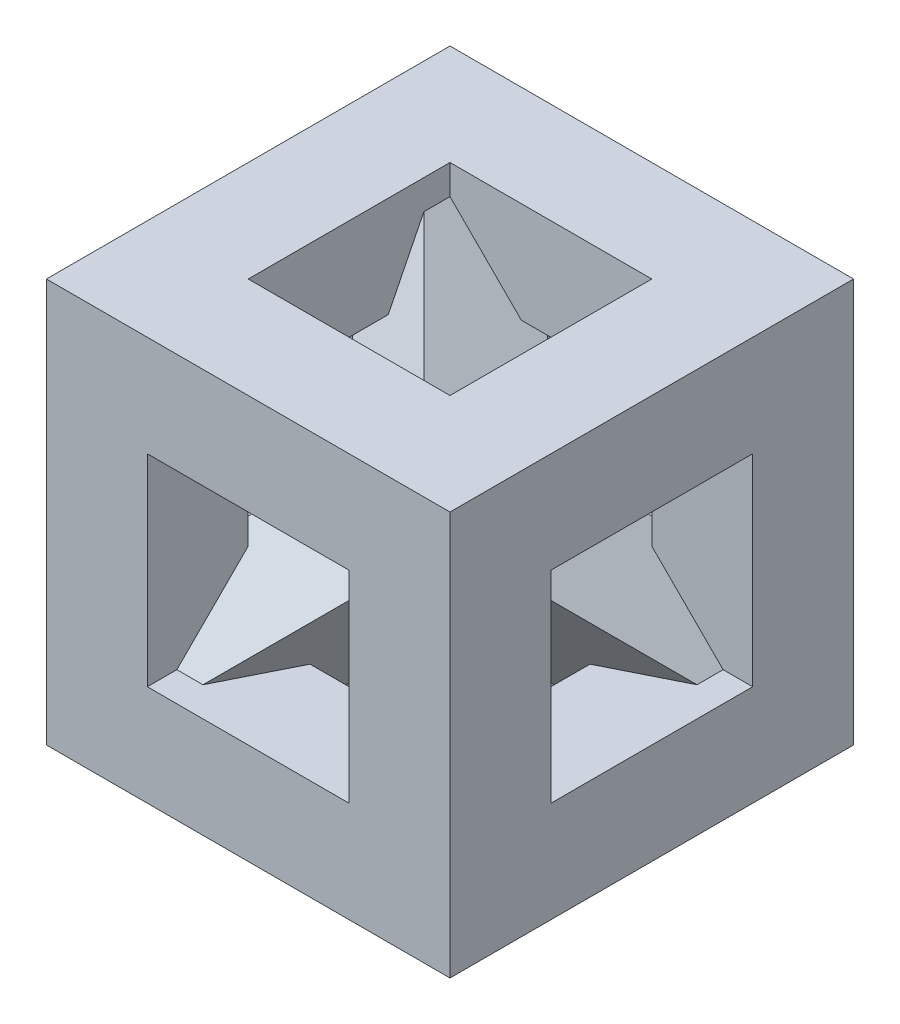
SolidWorks part; units mm, degrees
ref_plane "Front Plane" through (0, 0, 0) normal (0, 0, 1) x (1, 0, 0)
ref_plane "Top Plane" through (0, 0, 0) normal (0, 1, 0) x (1, 0, 0)
ref_plane "Right Plane" through (0, 0, 0) normal (1, 0, 0) x (0, 0, -1)
sketch "Sketch1" plane through (0, 0, 0) normal (0, 0, 1) x (1, 0, 0)
  line L1 (-5, 5) -> (5, 5)
  line L2 (-5, 5) -> (-5, -5)
  line L3 (-5, -5) -> (5, -5)
  line L4 (5, 5) -> (5, -5)
  line L5 (-5, 5) -> (5, -5) construction
  line L6 (-5, -5) -> (5, 5) construction
  point P0 (0, 0)
  dimension "D1" = 10
  dimension "D2" = 10
extrude "Boss-Extrude1" add sketch "Sketch1" along normal blind 10
sketch "Sketch2" plane through (0, 0, 10) normal (0, 0, 1) x (1, 0, 0)
  line L1 (-2.5, 2.5) -> (2.5, 2.5)
  line L2 (-2.5, 2.5) -> (-2.5, -2.5)
  line L3 (-2.5, -2.5) -> (2.5, -2.5)
  line L4 (2.5, 2.5) -> (2.5, -2.5)
  line L5 (-2.5, 2.5) -> (2.5, -2.5) construction
  line L6 (-2.5, -2.5) -> (2.5, 2.5) construction
  point P0 (0, 0)
  dimension "D1" = 5
extrude "Cut-Extrude1" cut sketch "Sketch2" against normal blind 13
sketch "Sketch3" plane through (5, 0, 0) normal (1, 0, 0) x (0, 0, -1)
  line L0 (0, -5) -> (0, 5) construction
  line L1 (-7.5, 2.5) -> (-2.5, 2.5)
  line L2 (-7.5, 2.5) -> (-7.5, -2.5)
  line L3 (-7.5, -2.5) -> (-2.5, -2.5)
  line L4 (-2.5, 2.5) -> (-2.5, -2.5)
  line L5 (-7.5, 2.5) -> (-2.5, -2.5) construction
  line L6 (-7.5, -2.5) -> (-2.5, 2.5) construction
  line L8 (-10, -5) -> (0, -5) construction
  point P0 (-5, 0)
  dimension "D1" = 5
  dimension "D2" = 2.5
  dimension "D3" = 2.5
extrude "Cut-Extrude2" cut sketch "Sketch3" against normal blind 13
sketch "Sketch4" plane through (0, 5, 0) normal (0, 1, 0) x (1, 0, 0)
  line L0 (5, -10) -> (-5, -10) construction
  line L2 (-5, -10) -> (-5, 0) construction
  line L7 (-2.5, -2.5) -> (2.5, -2.5)
  line L8 (-2.5, -2.5) -> (-2.5, -7.5)
  line L9 (-2.5, -7.5) -> (2.5, -7.5)
  line L10 (2.5, -2.5) -> (2.5, -7.5)
  line L11 (-2.5, -2.5) -> (2.5, -7.5) construction
  line L12 (-2.5, -7.5) -> (2.5, -2.5) construction
  dimension "D1" = 5
  dimension "D2" = 2.5
  dimension "D3" = 2.5
extrude "Cut-Extrude3" cut sketch "Sketch4" against normal blind 13
ref_plane "Plane5" through (-5, -5, 5) normal (-0.5774, -0.5774, 0.5774) x (-0.8165, 0.4082, -0.4082)
sketch "Sketch5" plane through (-5, -5, 5) normal (-0.5774, -0.5774, 0.5774) x (-0.8165, 0.4082, -0.4082)
  line L1 (-3.2912, -2.2855) -> (-0.7912, -2.2855)
  line L2 (-3.2912, -2.2855) -> (-3.2912, -4.7855)
  line L3 (-3.2912, -4.7855) -> (-0.7912, -4.7855)
  line L4 (-0.7912, -2.2855) -> (-0.7912, -4.7855)
  line L5 (-3.2912, -2.2855) -> (-0.7912, -4.7855) construction
  line L6 (-3.2912, -4.7855) -> (-0.7912, -2.2855) construction
  point P0 (-2.0412, -3.5355)
  dimension "D1" = 2.5
extrude "Boss-Extrude3" add sketch "Sketch5" against normal blind 12
ref_plane "Plane7" through (-1.6667, 1.6667, -1.6667) normal (-0.5774, 0.5774, -0.5774) x (-0.4082, 0.4082, 0.8165)
sketch "Sketch7" plane through (-1.6667, 1.6667, -1.6667) normal (-0.5774, 0.5774, -0.5774) x (-0.4082, 0.4082, 0.8165)
  line L1 (2.8325, 1.25) -> (5.3325, 1.25)
  line L2 (2.8325, 1.25) -> (2.8325, -1.25)
  line L3 (2.8325, -1.25) -> (5.3325, -1.25)
  line L4 (5.3325, 1.25) -> (5.3325, -1.25)
  line L5 (2.8325, 1.25) -> (5.3325, -1.25) construction
  line L6 (2.8325, -1.25) -> (5.3325, 1.25) construction
  point P0 (4.0825, 0)
  dimension "D1" = 2.5
extrude "Boss-Extrude4" add sketch "Sketch7" against normal blind 12
ref_plane "Plane9" through (-5, 5, 5) normal (-0.5774, 0.5774, 0.5774) x (0.4082, -0.4082, 0.8165)
sketch "Sketch9" plane through (-5, 5, 5) normal (-0.5774, 0.5774, 0.5774) x (0.4082, -0.4082, 0.8165)
  line L1 (2.8325, 1.25) -> (5.3325, 1.25)
  line L2 (2.8325, 1.25) -> (2.8325, -1.25)
  line L3 (2.8325, -1.25) -> (5.3325, -1.25)
  line L4 (5.3325, 1.25) -> (5.3325, -1.25)
  line L5 (2.8325, 1.25) -> (5.3325, -1.25) construction
  line L6 (2.8325, -1.25) -> (5.3325, 1.25) construction
  point P0 (4.0825, 0)
  dimension "D1" = 2.5
extrude "Boss-Extrude5" add sketch "Sketch9" against normal blind 12
ref_plane "Plane11" through (5, 5, 5) normal (0.5774, 0.5774, 0.5774) x (0.8165, -0.4082, -0.4082)
sketch "Sketch11" plane through (5, 5, 5) normal (0.5774, 0.5774, 0.5774) x (0.8165, -0.4082, -0.4082)
  line L1 (-3.2912, -2.2855) -> (-0.7912, -2.2855)
  line L2 (-3.2912, -2.2855) -> (-3.2912, -4.7855)
  line L3 (-3.2912, -4.7855) -> (-0.7912, -4.7855)
  line L4 (-0.7912, -2.2855) -> (-0.7912, -4.7855)
  line L5 (-3.2912, -2.2855) -> (-0.7912, -4.7855) construction
  line L6 (-3.2912, -4.7855) -> (-0.7912, -2.2855) construction
  point P0 (-2.0412, -3.5355)
  dimension "D1" = 2.5
extrude "Boss-Extrude6" add sketch "Sketch11" against normal blind 12
